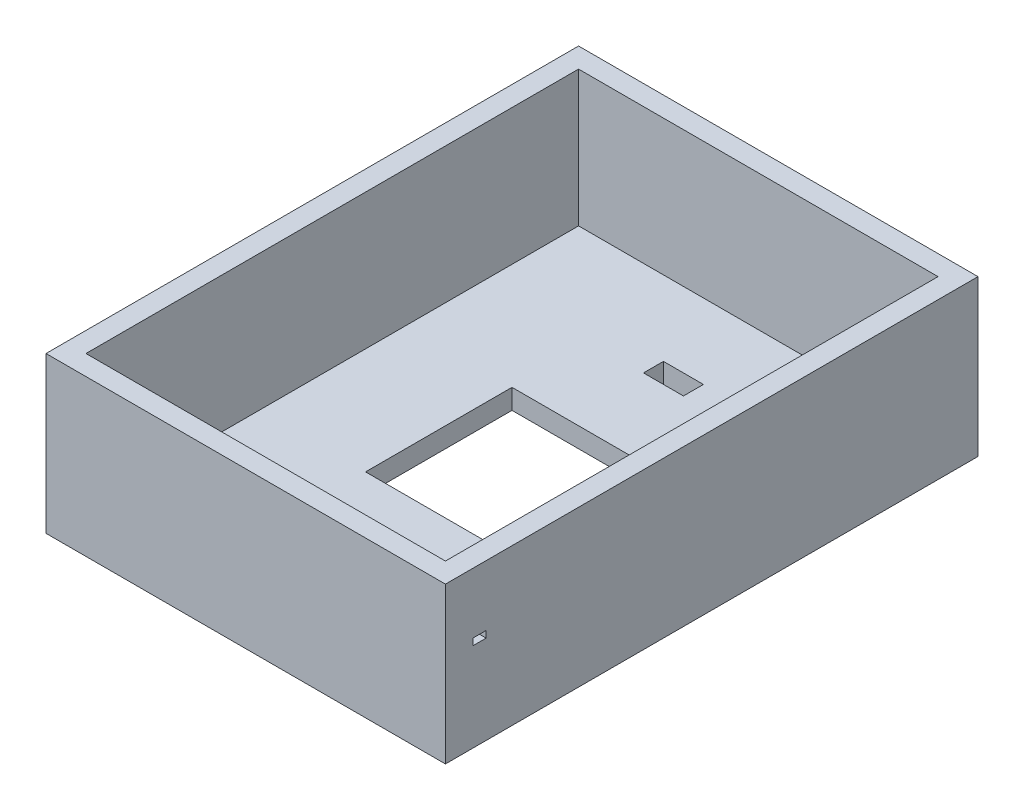
SolidWorks part; units mm, degrees
ref_plane "Front Plane" through (0, 0, 0) normal (0, 0, 1) x (1, 0, 0)
ref_plane "Top Plane" through (0, 0, 0) normal (0, 1, 0) x (1, 0, 0)
ref_plane "Right Plane" through (0, 0, 0) normal (1, 0, 0) x (0, 0, -1)
sketch "Sketch1" plane through (0, 0, 0) normal (0, 1, 0) x (1, 0, 0)
  line L1 (-150, -200) -> (150, -200)
  line L2 (-150, -200) -> (-150, 200)
  line L3 (-150, 200) -> (150, 200)
  line L4 (150, -200) -> (150, 200)
  line L5 (-150, -200) -> (150, 200) construction
  line L6 (-150, 200) -> (150, -200) construction
  point P0 (0, 0)
  dimension "D1" = 400
  dimension "D2" = 300
extrude "Boss-Extrude2" add sketch "Sketch1" along normal blind 117
sketch "Sketch3" plane through (0, 117, 0) normal (0, 1, 0) x (1, 0, 0)
  line L1 (-55, -55) -> (55, -55)
  line L2 (-55, -55) -> (-55, 55)
  line L3 (-55, 55) -> (55, 55)
  line L4 (55, -55) -> (55, 55)
  line L5 (-55, -55) -> (55, 55) construction
  line L6 (-55, 55) -> (55, -55) construction
  point P0 (0, 0)
  dimension "D1" = 110
  dimension "D2" = 110
extrude "Cut-Extrude2" cut sketch "Sketch3" against normal blind 117
sketch "Sketch5" plane through (0, 117, 0) normal (0, 1, 0) x (1, 0, 0)
  line L1 (-135, -185) -> (135, -185)
  line L2 (-135, -185) -> (-135, 185)
  line L3 (-135, 185) -> (135, 185)
  line L4 (135, -185) -> (135, 185)
  line L5 (-135, -185) -> (135, 185) construction
  line L6 (-135, 185) -> (135, -185) construction
  point P0 (0, 0)
  dimension "D1" = 370
  dimension "D2" = 270
extrude "Cut-Extrude3" cut sketch "Sketch5" against normal blind 102
sketch "Sketch7" plane through (0, 15, 0) normal (0, 1, 0) x (1, 0, 0)
  line L1 (-15, 128.7541) -> (15, 128.7541)
  line L2 (-15, 128.7541) -> (-15, 113.7541)
  line L3 (-15, 113.7541) -> (15, 113.7541)
  line L4 (15, 128.7541) -> (15, 113.7541)
  line L5 (-15, 128.7541) -> (15, 113.7541) construction
  line L6 (-15, 113.7541) -> (15, 128.7541) construction
  point P0 (0, 121.2541)
  dimension "D1" = 15
  dimension "D2" = 30
extrude "Cut-Extrude5" cut sketch "Sketch7" against normal blind 102
sketch "Sketch8" plane through (150, 0, 0) normal (1, 0, 0) x (0, 0, -1)
  line L1 (-179.4023, 71.5814) -> (-169.4023, 71.5814)
  line L2 (-179.4023, 71.5814) -> (-179.4023, 66.5814)
  line L3 (-179.4023, 66.5814) -> (-169.4023, 66.5814)
  line L4 (-169.4023, 71.5814) -> (-169.4023, 66.5814)
  line L5 (-179.4023, 71.5814) -> (-169.4023, 66.5814) construction
  line L6 (-179.4023, 66.5814) -> (-169.4023, 71.5814) construction
  point P0 (-174.4023, 69.0814)
  dimension "D1" = 5
  dimension "D2" = 10
extrude "Cut-Extrude7" cut sketch "Sketch8" against normal blind 90
sketch "Sketch9" plane through (-150, 0, 0) normal (-1, 0, 0) x (0, 0, 1)
  circle A0 centre (181.7407, 45.5273) radius 2.5
  circle A1 centre (165.2188, 45.5273) radius 2.5
  circle A2 centre (144.1534, 45.5273) radius 2.5
  circle A3 centre (123.088, 45.5273) radius 2.5
  dimension "D1" = 5
  dimension "D2" = 5
  dimension "D3" = 5
  dimension "D4" = 5
extrude "Cut-Extrude8" cut sketch "Sketch9" against normal blind 90
sketch "Sketch10" plane through (0, 15, 0) normal (0, 1, 0) x (1, 0, 0)
  circle A0 centre (114.5152, 165.9149) radius 4
  dimension "D1" = 8
extrude "Cut-Extrude9" cut sketch "Sketch10" against normal blind 90
